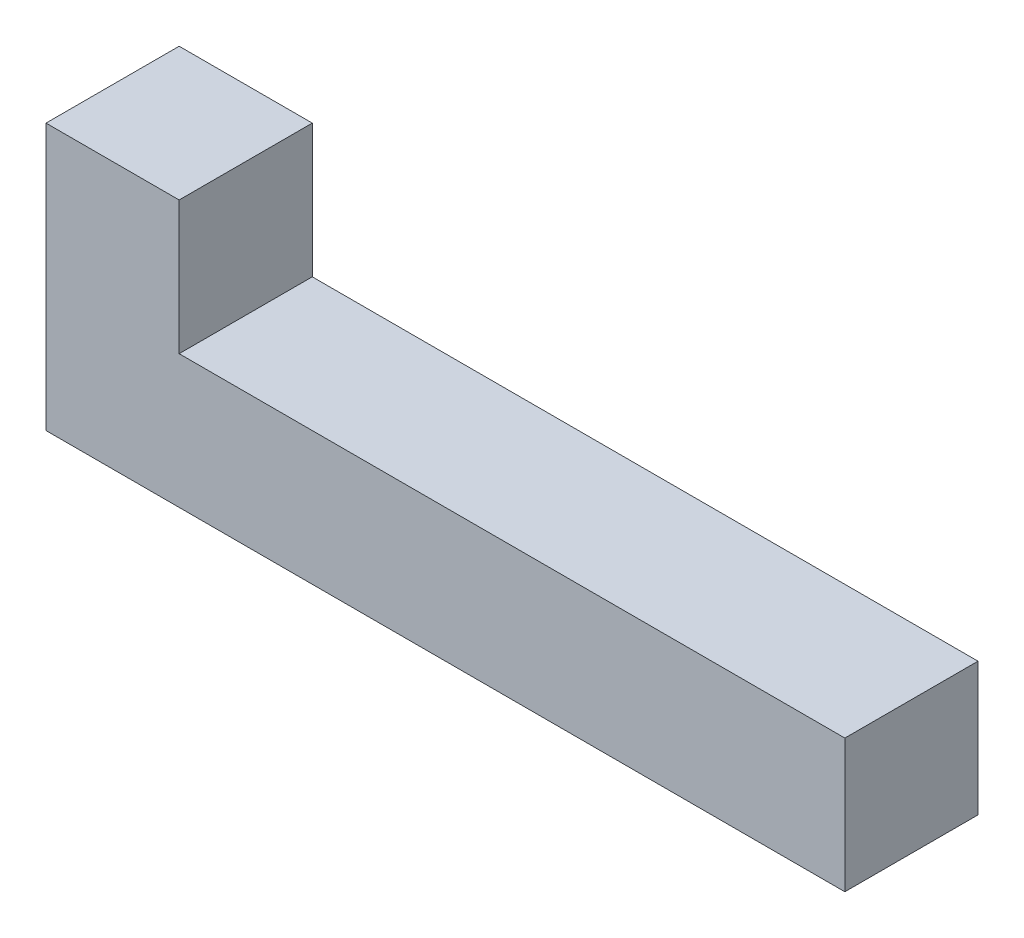
SolidWorks part; units mm, degrees
ref_plane "Plan de face" through (0, 0, 0) normal (0, 0, 1) x (1, 0, 0)
ref_plane "Plan de dessus" through (0, 0, 0) normal (0, 1, 0) x (1, 0, 0)
ref_plane "Plan de droite" through (0, 0, 0) normal (1, 0, 0) x (0, 0, -1)
sketch "Esquisse1" plane through (0, 0, 0) normal (0, 0, 1) x (1, 0, 0)
  line L1 (-4.7176, 0.5851) -> (25.2824, 0.5851)
  line L2 (-4.7176, 0.5851) -> (-4.7176, 5.5851)
  line L3 (-4.7176, 5.5851) -> (25.2824, 5.5851)
  line L4 (25.2824, 0.5851) -> (25.2824, 5.5851)
  line L5 (-4.7176, 5.5851) -> (0.2824, 5.5851)
  line L6 (-4.7176, 5.5851) -> (-4.7176, 10.5851)
  line L7 (-4.7176, 10.5851) -> (0.2824, 10.5851)
  line L8 (0.2824, 5.5851) -> (0.2824, 10.5851)
  dimension "D1" = 30
  dimension "D2" = 5
  dimension "D3" = 5
  dimension "D4" = 5
extrude "Boss.-Extru.1" add sketch "Esquisse1" along normal blind 5 contours L1 L4 L3 L2 | L3 L8 L7 L6
